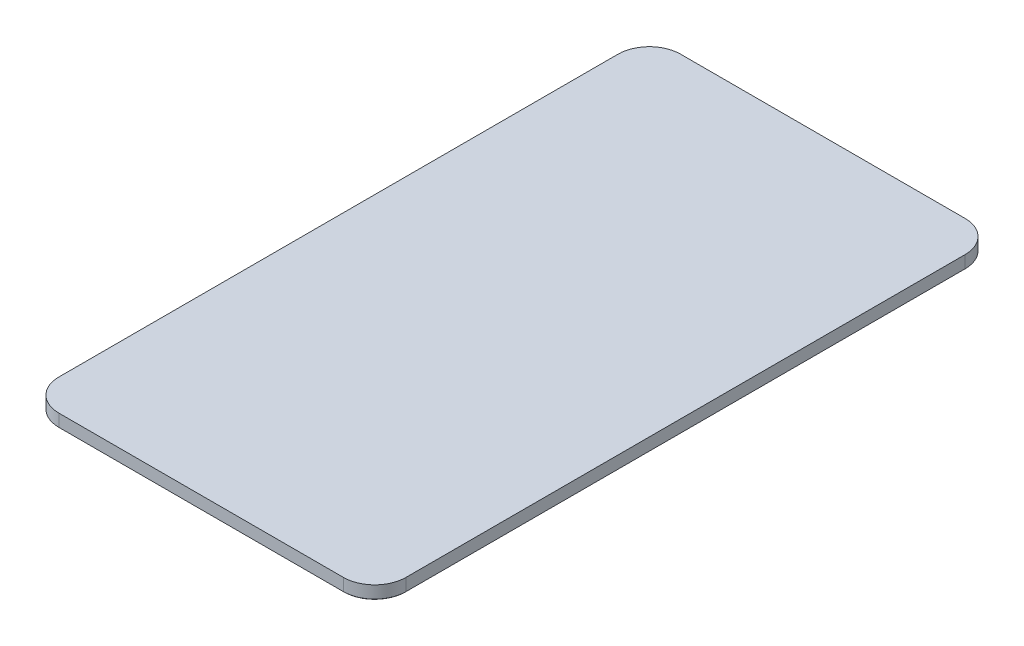
SolidWorks part; units mm, degrees
material "Acrylic (Medium-high impact)"
ref_plane "Front Plane" through (0, 0, 0) normal (0, 0, 1) x (1, 0, 0)
ref_plane "Top Plane" through (0, 0, 0) normal (0, 1, 0) x (1, 0, 0)
ref_plane "Right Plane" through (0, 0, 0) normal (1, 0, 0) x (0, 0, -1)
sketch "Sketch1" plane through (0, 0, 0) normal (0, 1, 0) x (1, 0, 0)
  line L1 (0, 0) -> (160.528, 0)
  line L2 (0, 0) -> (0, 287.528)
  line L3 (0, 287.528) -> (160.528, 287.528)
  line L4 (160.528, 0) -> (160.528, 287.528)
  dimension "D1" = 160.528
  dimension "D2" = 287.528
extrude "Boss-Extrude1" add sketch "Sketch1" along normal blind 5.969
fillet "Fillet2" radius 14.478 4 edges at (160.528, 2.9845, -287.528) (160.528, 2.9845, 0) (0, 2.9845, 0) (0, 2.9845, -287.528)
chamfer "Chamfer1" distance 0.254 angle 45 8 edges at (156.2875, 0, -4.2405) (80.264, 0, 0) (4.2405, 0, -4.2405) (0, 0, -143.764) (4.2405, 0, -283.2875) (80.264, 0, -287.528) (156.2875, 0, -283.2875) (160.528, 0, -143.764)
